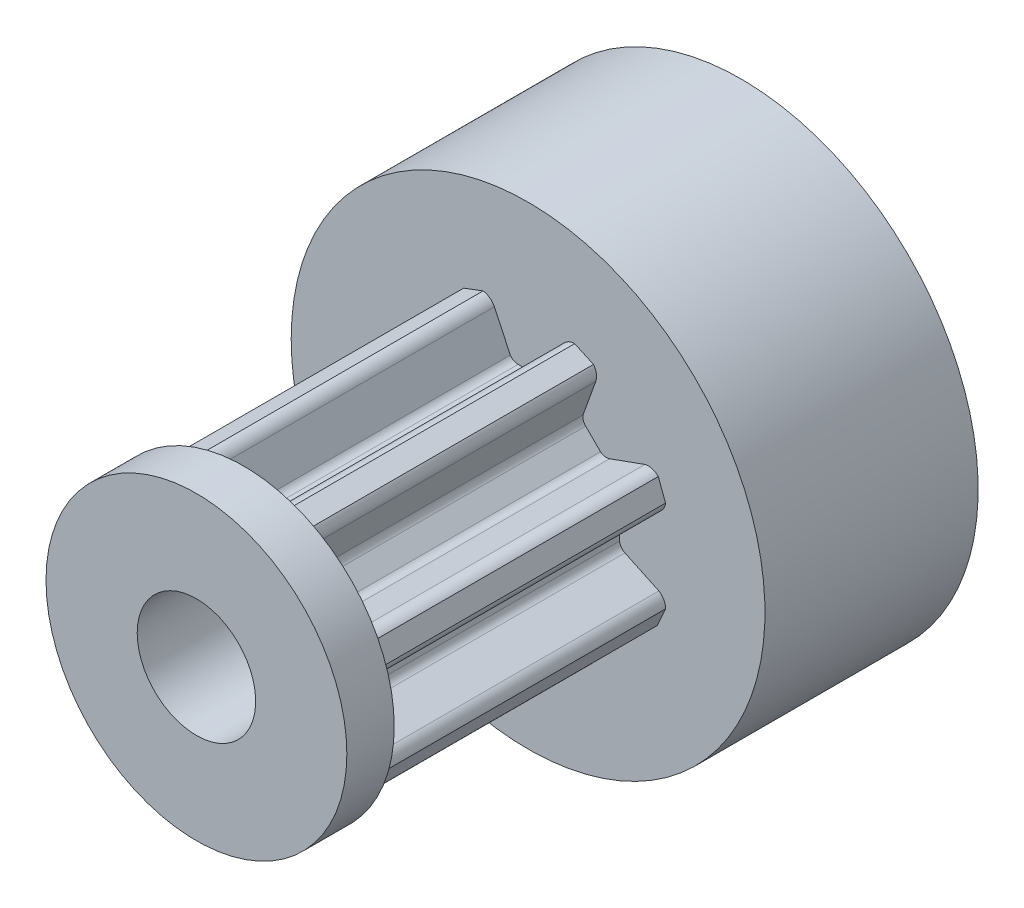
SolidWorks part; units mm, degrees
ref_plane "Front Plane" through (0, 0, 0) normal (0, 0, 1) x (1, 0, 0)
ref_plane "Top Plane" through (0, 0, 0) normal (0, 1, 0) x (1, 0, 0)
ref_plane "Right Plane" through (0, 0, 0) normal (1, 0, 0) x (0, 0, -1)
sketch "Sketch1" plane through (0, 0, 0) normal (0, 1, 0) x (1, 0, 0)
  line L0 (6.35, -12) -> (0, -12)
  line L1 (0, -12) -> (0, -14)
  line L2 (0, -14) -> (6.35, -14)
  line L3 (6.35, -14) -> (6.35, -12)
  line L4 (0, -12) -> (0, -14) construction
revolve "Revolve1" add sketch "Sketch1" angle 360 about L4
sketch "Sketch2" plane through (0, 0, 12) normal (0, 0, -1) x (-1, 0, 0)
  line L0 (-2.8752, -4.9328) -> (-2.3376, -3.4445)
  line L1 (-2.4004, -3.0587) -> (-3.0248, -2.4306)
  line L2 (-3.3789, -2.3198) -> (-4.8677, -2.8556)
  line L3 (-5.4464, -2.7613) -> (-5.8076, -1.9665)
  line L4 (-5.5211, -1.455) -> (-4.0885, -0.7827)
  line L5 (-3.8602, -0.4655) -> (-3.8576, 0.4202)
  line L6 (-4.0296, 0.7488) -> (-5.4612, 1.4228)
  line L7 (-5.8037, 1.8986) -> (-5.4971, 2.716)
  line L8 (-4.9328, 2.8752) -> (-3.4445, 2.3376)
  line L9 (-3.0587, 2.4004) -> (-2.4306, 3.0248)
  line L10 (-2.3198, 3.3789) -> (-2.8556, 4.8677)
  line L11 (-2.7613, 5.4464) -> (-1.9665, 5.8076)
  line L12 (-1.455, 5.5211) -> (-0.7827, 4.0885)
  line L13 (-0.4655, 3.8602) -> (0.4202, 3.8576)
  line L14 (0.7488, 4.0296) -> (1.4228, 5.4612)
  line L15 (1.8986, 5.8037) -> (2.716, 5.4971)
  line L16 (2.8752, 4.9328) -> (2.3376, 3.4445)
  line L17 (2.4004, 3.0587) -> (3.0248, 2.4306)
  line L18 (3.3789, 2.3198) -> (4.8677, 2.8556)
  line L19 (5.4464, 2.7613) -> (5.8076, 1.9665)
  line L20 (5.5211, 1.455) -> (4.0885, 0.7827)
  line L21 (3.8602, 0.4655) -> (3.8576, -0.4202)
  line L22 (4.0296, -0.7488) -> (5.4612, -1.4228)
  line L23 (5.8037, -1.8986) -> (5.4971, -2.716)
  line L24 (4.9328, -2.8752) -> (3.4445, -2.3376)
  line L25 (3.0587, -2.4004) -> (2.4306, -3.0248)
  line L26 (2.3198, -3.3789) -> (2.8556, -4.8677)
  line L27 (2.7613, -5.4464) -> (1.9665, -5.8076)
  line L28 (1.455, -5.5211) -> (0.7827, -4.0885)
  line L29 (0.4655, -3.8602) -> (-0.4202, -3.8576)
  line L30 (-0.7488, -4.0296) -> (-1.4228, -5.4612)
  line L31 (-1.8986, -5.8037) -> (-2.716, -5.4971)
  arc A0 (-2.716, -5.4971) -> (-2.8752, -4.9328) centre (-2.2918, -5.0729) cw
  arc A1 (-2.3376, -3.4445) -> (-2.4004, -3.0587) centre (-2.7253, -3.3096) ccw
  arc A2 (-3.0248, -2.4306) -> (-3.3789, -2.3198) centre (-3.3116, -2.7261) ccw
  arc A3 (-4.8677, -2.8556) -> (-5.4464, -2.7613) centre (-5.0716, -2.2838) cw
  arc A4 (-5.8076, -1.9665) -> (-5.5211, -1.455) centre (-5.2076, -1.9665) cw
  arc A5 (-4.0885, -0.7827) -> (-3.8602, -0.4655) centre (-4.2673, -0.4131) ccw
  arc A6 (-3.8576, 0.4202) -> (-4.0296, 0.7488) centre (-4.2694, 0.414) ccw
  arc A7 (-5.4612, 1.4228) -> (-5.8037, 1.8986) centre (-5.201, 1.9713) cw
  arc A8 (-5.4971, 2.716) -> (-4.9328, 2.8752) centre (-5.0729, 2.2918) cw
  arc A9 (-3.4445, 2.3376) -> (-3.0587, 2.4004) centre (-3.3096, 2.7253) ccw
  arc A10 (-2.4306, 3.0248) -> (-2.3198, 3.3789) centre (-2.7261, 3.3116) ccw
  arc A11 (-2.8556, 4.8677) -> (-2.7613, 5.4464) centre (-2.2838, 5.0716) cw
  arc A12 (-1.9665, 5.8076) -> (-1.455, 5.5211) centre (-1.9665, 5.2076) cw
  arc A13 (-0.7827, 4.0885) -> (-0.4655, 3.8602) centre (-0.4131, 4.2673) ccw
  arc A14 (0.4202, 3.8576) -> (0.7488, 4.0296) centre (0.414, 4.2694) ccw
  arc A15 (1.4228, 5.4612) -> (1.8986, 5.8037) centre (1.9713, 5.201) cw
  arc A16 (2.716, 5.4971) -> (2.8752, 4.9328) centre (2.2918, 5.0729) cw
  arc A17 (2.3376, 3.4445) -> (2.4004, 3.0587) centre (2.7253, 3.3096) ccw
  arc A18 (3.0248, 2.4306) -> (3.3789, 2.3198) centre (3.3116, 2.7261) ccw
  arc A19 (4.8677, 2.8556) -> (5.4464, 2.7613) centre (5.0716, 2.2838) cw
  arc A20 (5.8076, 1.9665) -> (5.5211, 1.455) centre (5.2076, 1.9665) cw
  arc A21 (4.0885, 0.7827) -> (3.8602, 0.4655) centre (4.2673, 0.4131) ccw
  arc A22 (3.8576, -0.4202) -> (4.0296, -0.7488) centre (4.2694, -0.414) ccw
  arc A23 (5.4612, -1.4228) -> (5.8037, -1.8986) centre (5.201, -1.9713) cw
  arc A24 (5.4971, -2.716) -> (4.9328, -2.8752) centre (5.0729, -2.2918) cw
  arc A25 (3.4445, -2.3376) -> (3.0587, -2.4004) centre (3.3096, -2.7253) ccw
  arc A26 (2.4306, -3.0248) -> (2.3198, -3.3789) centre (2.7261, -3.3116) ccw
  arc A27 (2.8556, -4.8677) -> (2.7613, -5.4464) centre (2.2838, -5.0716) cw
  arc A28 (1.9665, -5.8076) -> (1.455, -5.5211) centre (1.9665, -5.2076) cw
  arc A29 (0.7827, -4.0885) -> (0.4655, -3.8602) centre (0.4131, -4.2673) ccw
  arc A30 (-0.4202, -3.8576) -> (-0.7488, -4.0296) centre (-0.414, -4.2694) ccw
  arc A31 (-1.4228, -5.4612) -> (-1.8986, -5.8037) centre (-1.9713, -5.201) cw
extrude "Boss-Extrude1" add sketch "Sketch2" along normal blind 12
sketch "Sketch3" plane through (0, 0, 0) normal (0, 0, 1) x (1, 0, 0)
  circle A0 centre (0, 0) radius 10
extrude "Boss-Extrude2" add sketch "Sketch3" against normal blind 9
ref_plane "Plane1" through (0, 5, 0) normal (0, -1, 0) x (1, 0, 0)
ref_plane "Plane2" through (0, -5, 0) normal (0, 1, 0) x (1, 0, 0)
hole_wizard "Ø5.0 (5) Diameter Hole1" positions "Sketch11" profile "Sketch10" hole size "Ø5.0" standard "ANSI Metric"
sketch "Sketch11" plane through (0, 0, -9) normal (0, 0, -1) x (-1, 0, 0)
  point P0 (0, 0)
sketch "Sketch10" plane through (0, 0, -9) normal (1, 0, 0) x (0, 1, 0)
  line L0 (0, 0) -> (0, 23)
  line L1 (0, 23) -> (2.5, 23)
  line L2 (2.5, 23) -> (2.5, 0)
  line L5 (2.5, 0) -> (0, 0)
  line L11 (0, -6.35) -> (0, 107.95) construction
  dimension "Thru Hole Dia." = 5
  dimension "Thru Hole Depth" = 23
